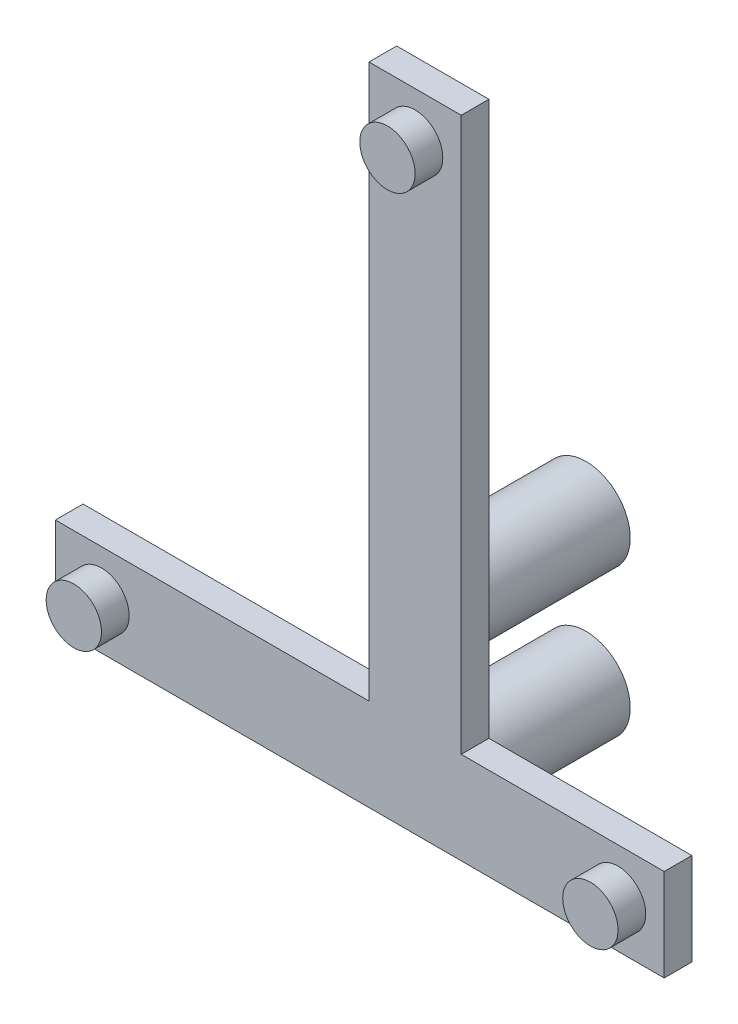
SolidWorks part; units mm, degrees
ref_plane "Front Plane" through (0, 0, 0) normal (0, 0, 1) x (1, 0, 0)
ref_plane "Top Plane" through (0, 0, 0) normal (0, 1, 0) x (1, 0, 0)
ref_plane "Right Plane" through (0, 0, 0) normal (1, 0, 0) x (0, 0, -1)
sketch "Sketch4" plane through (0, 0, 0) normal (0, 0, 1) x (1, 0, 0)
  line L0 (-139.5612, 16.0705) -> (-106.5612, 16.0705)
  line L1 (-106.5612, 16.0705) -> (-106.5612, 21.0705)
  line L2 (-106.5612, 21.0705) -> (-117.5612, 21.0705)
  line L3 (-117.5612, 21.0705) -> (-117.5612, 51.0705)
  line L4 (-117.5612, 51.0705) -> (-122.5612, 51.0705)
  line L5 (-122.5612, 51.0705) -> (-122.5612, 21.0705)
  line L6 (-122.5612, 21.0705) -> (-139.5612, 21.0705)
  line L7 (-139.5612, 21.0705) -> (-139.5612, 16.0705)
  dimension "D1" = 5
  dimension "D2" = 5
  dimension "D3" = 5
  dimension "D4" = 33
  dimension "D5" = 17
  dimension "D6" = 30
extrude "Boss-Extrude2" add sketch "Sketch4" along normal blind 1.5
sketch "Sketch5" plane through (0, 0, 0) normal (0, 0, -1) x (-1, 0, 0)
  line L0 (106.5612, 16.0705) -> (106.5612, 21.0705) construction
  line L1 (139.5612, 16.0705) -> (106.5612, 16.0705) construction
  line L2 (117.5612, 21.0705) -> (117.5612, 51.0705) construction
  circle A0 centre (137.0612, 18.5705) radius 1.5
  circle A1 centre (109.0612, 18.5705) radius 1.5
  circle A2 centre (120.0612, 48.5705) radius 1.5
  dimension "D1" = 28
  dimension "D2" = 3
  dimension "D3" = 3
  dimension "D4" = 2.5
  dimension "D5" = 2.5
  dimension "D6" = 2.5
  dimension "D7" = 3
  dimension "D8" = 30
  dimension "D9" = 2.5
extrude "Boss-Extrude5" add sketch "Sketch5" against normal blind 3
sketch "Sketch6" plane through (0, 0, 0) normal (0, 0, -1) x (-1, 0, 0)
  line L0 (139.5612, 16.0705) -> (106.5612, 16.0705) construction
  line L1 (117.5612, 21.0705) -> (117.5612, 51.0705) construction
  circle A0 centre (120.0612, 18.5705) radius 2.4
  circle A1 centre (120.0612, 26.5405) radius 2.4
  dimension "D1" = 4.8
  dimension "D2" = 4.8
  dimension "D3" = 2.5
  dimension "D4" = 2.5
  dimension "D5" = 2.5
  dimension "D6" = 7.97
extrude "Boss-Extrude6" add sketch "Sketch6" along normal blind 7.76
